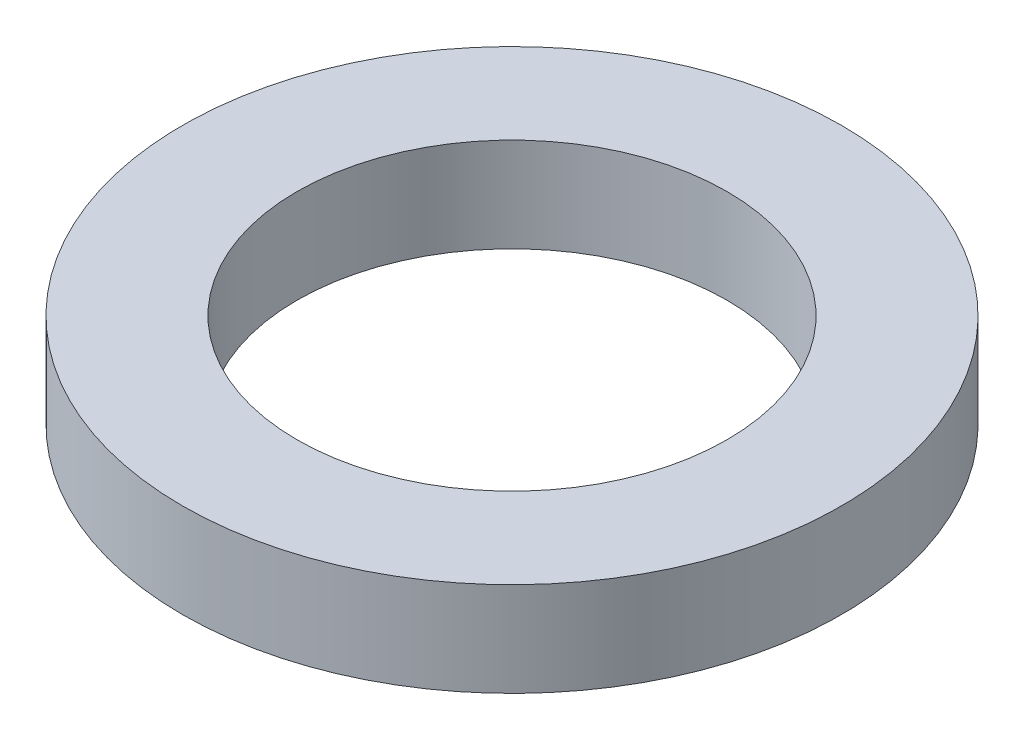
SolidWorks part; units mm, degrees
ref_plane "Front Plane" through (0, 0, 0) normal (0, 0, 1) x (1, 0, 0)
ref_plane "Top Plane" through (0, 0, 0) normal (0, 1, 0) x (1, 0, 0)
ref_plane "Right Plane" through (0, 0, 0) normal (1, 0, 0) x (0, 0, -1)
sketch "Sketch1" plane through (0, 0, 0) normal (0, 1, 0) x (1, 0, 0)
  circle A0 centre (0, 0) radius 14.5
  circle A1 centre (0, 0) radius 22.225
  dimension "D1" = 29
  dimension "D2" = 44.45
extrude "Boss-Extrude1" add sketch "Sketch1" along normal blind 6.35
